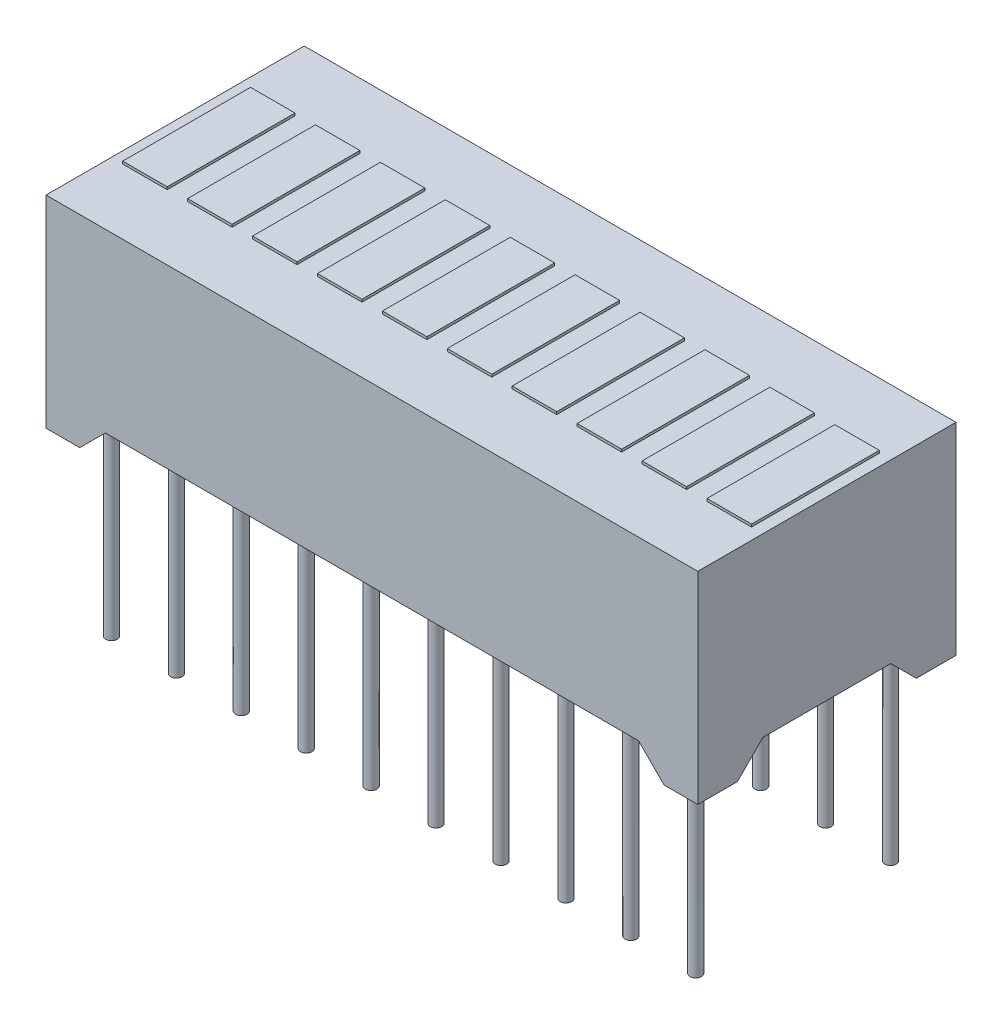
SolidWorks part; units mm, degrees
ref_plane "Alzado" through (0, 0, 0) normal (0, 0, 1) x (1, 0, 0)
ref_plane "Planta" through (0, 0, 0) normal (0, 1, 0) x (1, 0, 0)
ref_plane "Vista lateral" through (0, 0, 0) normal (1, 0, 0) x (0, 0, -1)
sketch "Croquis2" plane through (0, 0, 0) normal (0, 1, 0) x (1, 0, 0)
  line L1 (0, 0) -> (25.5, 0)
  line L2 (0, 0) -> (0, 10.1)
  line L3 (0, 10.1) -> (25.5, 10.1)
  line L4 (25.5, 0) -> (25.5, 10.1)
  dimension "D1" = 10.1
  dimension "D2" = 25.5
extrude "Saliente-Extruir2" add sketch "Croquis2" along normal blind 7.9
sketch "Croquis3" plane through (25.5, 0, 0) normal (1, 0, 0) x (0, 0, -1)
  line L0 (1.55, 0) -> (2.55, 1)
  line L1 (0, 0) -> (10.1, 0) construction
  line L2 (2.55, 1) -> (7.55, 1)
  line L3 (5.05, 0) -> (5.05, 2.7828) construction
  line L4 (8.55, 0) -> (7.55, 1)
  line L5 (1.55, 0) -> (8.55, 0)
  point P9 (5.05, 1)
  dimension "D1" = 1
  dimension "D2" = 2.5
  dimension "D3" = 45
extrude "Cortar-Extruir1" cut sketch "Croquis3" against normal through all
sketch "Croquis4" plane through (0, 7.9, 0) normal (0, 1, 0) x (1, 0, 0)
  line L0 (0, 5.05) -> (25.5, 5.05) construction
  line L1 (0.45, 7.55) -> (2.19, 7.55)
  line L2 (0.45, 7.55) -> (0.45, 2.55)
  line L3 (0.45, 2.55) -> (2.19, 2.55)
  line L4 (2.19, 7.55) -> (2.19, 2.55)
  line L5 (0, 10.1) -> (0, 0) construction
  line L6 (25.5, 0) -> (25.5, 10.1) construction
  line L7 (2.99, 7.55) -> (4.73, 7.55)
  line L8 (2.99, 7.55) -> (2.99, 2.55)
  line L9 (2.99, 2.55) -> (4.73, 2.55)
  line L10 (4.73, 7.55) -> (4.73, 2.55)
  line L11 (5.53, 7.55) -> (7.27, 7.55)
  line L12 (5.53, 7.55) -> (5.53, 2.55)
  line L13 (5.53, 2.55) -> (7.27, 2.55)
  line L14 (7.27, 7.55) -> (7.27, 2.55)
  line L15 (8.07, 7.55) -> (9.81, 7.55)
  line L16 (8.07, 7.55) -> (8.07, 2.55)
  line L17 (8.07, 2.55) -> (9.81, 2.55)
  line L18 (9.81, 7.55) -> (9.81, 2.55)
  line L19 (10.61, 7.55) -> (12.35, 7.55)
  line L20 (10.61, 7.55) -> (10.61, 2.55)
  line L21 (10.61, 2.55) -> (12.35, 2.55)
  line L22 (12.35, 7.55) -> (12.35, 2.55)
  line L23 (13.15, 7.55) -> (14.89, 7.55)
  line L24 (13.15, 7.55) -> (13.15, 2.55)
  line L25 (13.15, 2.55) -> (14.89, 2.55)
  line L26 (14.89, 7.55) -> (14.89, 2.55)
  line L27 (15.69, 7.55) -> (17.43, 7.55)
  line L28 (15.69, 7.55) -> (15.69, 2.55)
  line L29 (15.69, 2.55) -> (17.43, 2.55)
  line L30 (17.43, 7.55) -> (17.43, 2.55)
  line L31 (18.23, 7.55) -> (19.97, 7.55)
  line L32 (18.23, 7.55) -> (18.23, 2.55)
  line L33 (18.23, 2.55) -> (19.97, 2.55)
  line L34 (19.97, 7.55) -> (19.97, 2.55)
  line L35 (20.77, 7.55) -> (22.51, 7.55)
  line L36 (20.77, 7.55) -> (20.77, 2.55)
  line L37 (20.77, 2.55) -> (22.51, 2.55)
  line L38 (22.51, 7.55) -> (22.51, 2.55)
  line L39 (23.31, 7.55) -> (25.05, 7.55)
  line L40 (23.31, 7.55) -> (23.31, 2.55)
  line L41 (23.31, 2.55) -> (25.05, 2.55)
  line L42 (25.05, 7.55) -> (25.05, 2.55)
  point P10 (0.45, 5.05)
  dimension "D1" = 5
  dimension "D2" = 1.74
  dimension "D3" = 0.45
  dimension "D4" = 10
extrude "Saliente-Extruir3" add sketch "Croquis4" along normal blind 0.1
sketch "Croquis6" plane through (0, 0, -10.1) normal (0, 0, -1) x (-1, 0, 0)
  line L0 (-24.18, 0) -> (-23.18, 1)
  line L1 (-25.5, 0) -> (0, 0) construction
  line L2 (-23.18, 1) -> (-2.32, 1)
  line L3 (-12.75, 0) -> (-12.75, 9.3383) construction
  line L4 (0, 1) -> (-25.5, 1) construction
  line L5 (0, 1) -> (-25.5, 1) construction
  line L6 (-25.05, 8) -> (-23.31, 8) construction
  line L7 (-25.05, 8) -> (-23.31, 8)
  line L8 (-24.18, 8) -> (-24.18, -2.3524) construction
  line L9 (-1.32, 0) -> (-2.32, 1)
  line L10 (-24.18, 0) -> (-1.32, 0)
  point P17 (-12.75, 1)
  line M6 (-25.5, 0) -> (0, 0)
  dimension "D1" = 45
extrude "Cortar-Extruir2" cut sketch "Croquis6" against normal through all contours L9 L2 L0 M6
sketch "Croquis7" plane through (0, 0, 0) normal (0, -1, 0) x (1, 0, 0)
  line L0 (0, -5.05) -> (25.5, -5.05) construction
  line L1 (0, -7.55) -> (0, -2.55) construction
  line L2 (25.5, -7.55) -> (25.5, -2.55) construction
  line L3 (12.75, 0) -> (12.75, -10.1) construction
  line L4 (23.18, 0) -> (2.32, 0) construction
  line L5 (23.18, -10.1) -> (2.32, -10.1) construction
  circle A0 centre (1.32, -8.86) radius 0.225
  circle A1 centre (3.86, -8.86) radius 0.225
  circle A2 centre (6.4, -8.86) radius 0.225
  circle A3 centre (8.94, -8.86) radius 0.225
  circle A4 centre (11.48, -8.86) radius 0.225
  circle A5 centre (14.02, -8.86) radius 0.225
  circle A6 centre (16.56, -8.86) radius 0.225
  circle A7 centre (19.1, -8.86) radius 0.225
  circle A8 centre (21.64, -8.86) radius 0.225
  circle A9 centre (24.18, -8.86) radius 0.225
  circle A10 centre (3.86, -1.24) radius 0.225
  circle A11 centre (6.4, -1.24) radius 0.225
  circle A12 centre (8.94, -1.24) radius 0.225
  circle A13 centre (11.48, -1.24) radius 0.225
  circle A14 centre (14.02, -1.24) radius 0.225
  circle A15 centre (16.56, -1.24) radius 0.225
  circle A16 centre (19.1, -1.24) radius 0.225
  circle A17 centre (21.64, -1.24) radius 0.225
  circle A18 centre (24.18, -1.24) radius 0.225
  circle A19 centre (1.32, -1.24) radius 0.225
  dimension "D2" = 0.45
  dimension "D1" = 3.81
  dimension "D3" = 22.86
  dimension "D4" = 10
  dimension "D5" = 2
extrude "Saliente-Extruir4" add sketch "Croquis7" along normal blind 7 and the other way up to next
